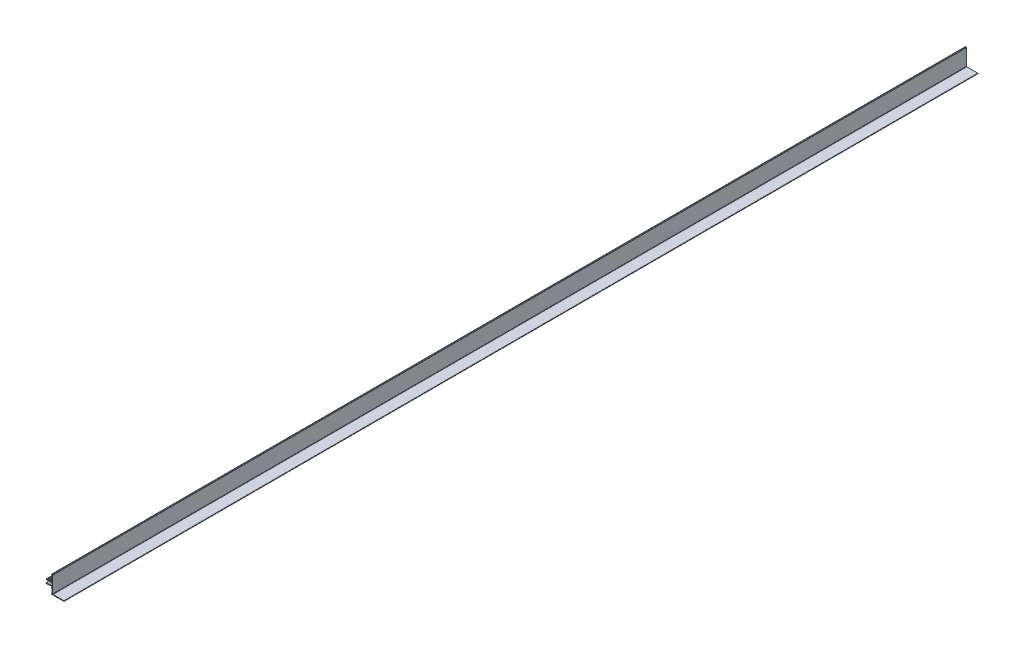
SolidWorks part; units mm, degrees
material "ABS (Black)"
ref_plane "Front" through (0, 0, 0) normal (0, 0, 1) x (1, 0, 0)
ref_plane "Top" through (0, 0, 0) normal (0, 1, 0) x (1, 0, 0)
ref_plane "Right" through (0, 0, 0) normal (1, 0, 0) x (0, 0, -1)
sketch "Sk Main Extrusion" plane through (0, 0, 0) normal (0, 0, 1) x (1, 0, 0)
  line L0 (-3.83, 2.5328) -> (-11.3125, 2.9251)
  line L5 (-3.83, -2.5328) -> (-11.3125, -2.9251)
  line L6 (1.1989, -5.1201) -> (1.67, -5.1201)
  line L7 (1.1989, -7.8799) -> (1.67, -7.8799)
  line L8 (1.1989, 7.8799) -> (1.67, 7.8799)
  line L9 (1.1989, 5.1201) -> (1.67, 5.1201)
  line L10 (1.67, -5.1201) -> (1.67, -7.8799) construction
  line L11 (1.67, -7.8799) -> (1.67, -17.05)
  line L12 (0.92, 17.8) -> (0.663, 17.8)
  line L13 (0.663, -17.8) -> (0.663, -19.05) construction
  line L14 (1.67, 7.8799) -> (1.67, 5.1201) construction
  line L15 (0, 0) -> (1.67, 0) construction
  line L16 (2.17, 19.05) -> (0.663, 19.05)
  line L17 (1.67, 17.05) -> (1.67, 7.8799)
  line L18 (0.663, 19.05) -> (0.663, 17.8) construction
  line L19 (1.67, 17.05) -> (2.92, 17.05) construction
  line L20 (0.663, -19.05) -> (27.295, -19.05)
  line L21 (3.67, -17.8) -> (27.295, -17.8)
  line L22 (27.295, -17.8) -> (27.295, -19.05) construction
  line L23 (0.038, 6.5) -> (1.67, 6.5) construction
  line L24 (0.038, 6.65) -> (0.038, 6.35)
  line L25 (1.67, 5.1201) -> (1.67, 3.625)
  line L26 (1.67, 3.625) -> (-3.83, 3.625)
  line L27 (-4.23, 4.025) -> (-4.23, 4.56)
  line L28 (-4.23, 4.56) -> (-4.9341, 5)
  line L29 (-4.9341, 5) -> (-5.4741, 5)
  line L30 (-5.4741, 5) -> (-8.08, 4.3)
  line L31 (-8.08, 4.3) -> (-9.58, 4.3)
  line L32 (-9.58, 4.3) -> (-10.1001, 4.625)
  line L33 (-10.1001, 4.625) -> (-11.5147, 3.9654)
  line L34 (-3.83, 2.5328) -> (1.67, 2.4368)
  line L35 (1.67, 2.4368) -> (1.67, -2.4368)
  line L36 (1.67, -2.4368) -> (-3.83, -2.5328)
  line L37 (-11.5147, -3.9654) -> (-10.1001, -4.625)
  line L38 (-10.1001, -4.625) -> (-9.58, -4.3)
  line L39 (-9.58, -4.3) -> (-8.08, -4.3)
  line L40 (-8.08, -4.3) -> (-5.4741, -5)
  line L41 (-5.4741, -5) -> (-4.9341, -5)
  line L42 (-4.9341, -5) -> (-4.23, -4.56)
  line L43 (-4.23, -4.56) -> (-4.23, -4.025)
  line L44 (-3.83, -3.625) -> (1.67, -3.625)
  line L45 (1.67, -3.625) -> (1.67, -5.1201)
  line L46 (0.038, -6.35) -> (0.038, -6.65)
  line L47 (0.92, -17.8) -> (0.663, -17.8)
  line L48 (2.92, -17.05) -> (2.92, 18.3)
  arc A0 (0.92, 17.8) -> (1.67, 17.05) centre (0.92, 17.05) cw
  arc A1 (0.663, 17.8) -> (0.663, 19.05) centre (0.663, 18.425) cw
  arc A2 (3.67, -17.8) -> (2.92, -17.05) centre (3.67, -17.05) cw
  arc A3 (0.663, -19.05) -> (0.663, -17.8) centre (0.663, -18.425) cw
  arc A4 (27.295, -19.05) -> (27.295, -17.8) centre (27.295, -18.425) ccw
  arc A5 (1.67, -17.05) -> (0.92, -17.8) centre (0.92, -17.05) cw
  arc A6 (2.17, 19.05) -> (2.92, 18.3) centre (2.17, 18.3) cw
  arc A7 (1.1989, 7.8799) -> (0.038, 6.65) centre (1.27, 6.65) ccw
  arc A8 (0.038, 6.35) -> (1.1989, 5.1201) centre (1.27, 6.35) ccw
  arc A9 (-4.23, 4.025) -> (-3.83, 3.625) centre (-3.83, 4.025) ccw
  arc A10 (-11.5147, 3.9654) -> (-11.3125, 2.9251) centre (-11.2839, 3.4704) ccw
  arc A11 (-11.3125, -2.9251) -> (-11.5147, -3.9654) centre (-11.2839, -3.4704) ccw
  arc A12 (-3.83, -3.625) -> (-4.23, -4.025) centre (-3.83, -4.025) ccw
  arc A13 (1.1989, -5.1201) -> (0.038, -6.35) centre (1.27, -6.35) ccw
  arc A14 (0.038, -6.65) -> (1.1989, -7.8799) centre (1.27, -6.65) ccw
  point P55 (0, 0)
  point P56 (0.038, 18.425)
  point P58 (1.67, 0)
  point P69 (0.038, -18.425)
extrude "Main Extrusion" add sketch "Sk Main Extrusion" against normal blind 2000
equation "\"Weight kg\"= round ( \"SW-Mass\" , 2 )"
equation "\"Weight lbs\"= round ( \"SW-Mass\" * 2.2046 , 2 )"
equation "\"Length mm\"= round ( \"Length@Main Extrusion\" , 2 )"
equation "\"Length in\"= round ( \"Length@Main Extrusion\" / 25.4 , 3 )"
